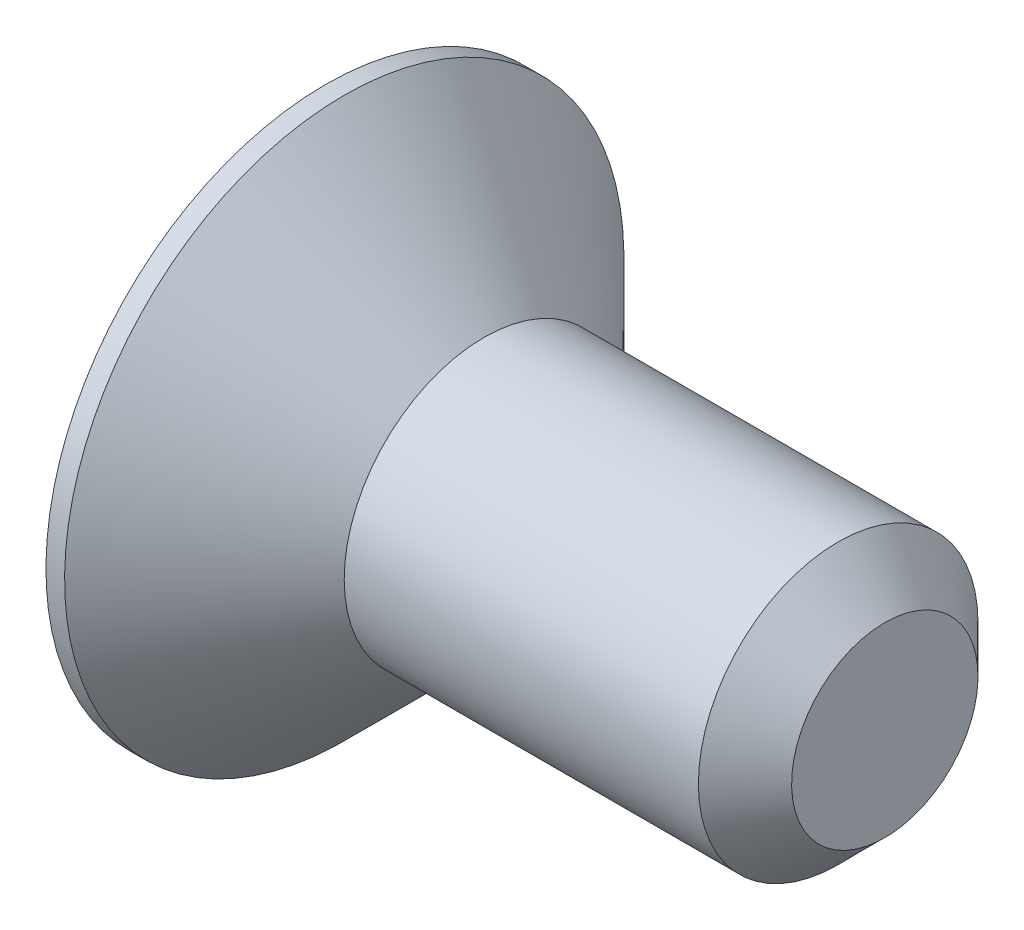
SolidWorks part; units mm, degrees
ref_plane "Plan de face" through (0, 0, 0) normal (0, 0, 1) x (1, 0, 0)
ref_plane "Plan de dessus" through (0, 0, 0) normal (0, 1, 0) x (1, 0, 0)
ref_plane "Plan de droite" through (0, 0, 0) normal (1, 0, 0) x (0, 0, -1)
sketch "Esquisse1" plane through (0, 0, 0) normal (0, 0, 1) x (1, 0, 0)
  line L0 (0, 0) -> (0, 3)
  line L1 (0, 3) -> (0.2, 3)
  line L2 (0.2, 3) -> (1.7, 1.5)
  line L3 (1.7, 1.5) -> (6, 1.5)
  line L4 (6, 1.5) -> (6, 0)
  line L5 (6, 0) -> (0, 0) construction
  line L6 (0, 0) -> (6, 0)
  dimension "D1" = 1.7
  dimension "D2" = 6
  dimension "D3" = 3
  dimension "D4" = 6
  dimension "D5" = 45
revolve "Révolution1" add sketch "Esquisse1" angle 360 about L5
chamfer "Chanfrein1" distance 0.5 angle 45 1 edges at (6, 1.5, 0)
sketch "Esquisse2" plane through (0, 0, 0) normal (-1, 0, 0) x (0, 0, 1)
  line L1 (0, 1.1547) -> (-1, 0.5774)
  line L2 (-1, 0.5774) -> (-1, -0.5774)
  line L3 (-1, -0.5774) -> (0, -1.1547)
  line L4 (0, -1.1547) -> (1, -0.5774)
  line L5 (1, -0.5774) -> (1, 0.5774)
  line L6 (1, 0.5774) -> (0, 1.1547)
  circle A0 centre (0, 0) radius 1 construction
  dimension "D1" = 2
extrude "Enlèv. mat.-Extru.1" cut sketch "Esquisse2" against normal blind 1.2
